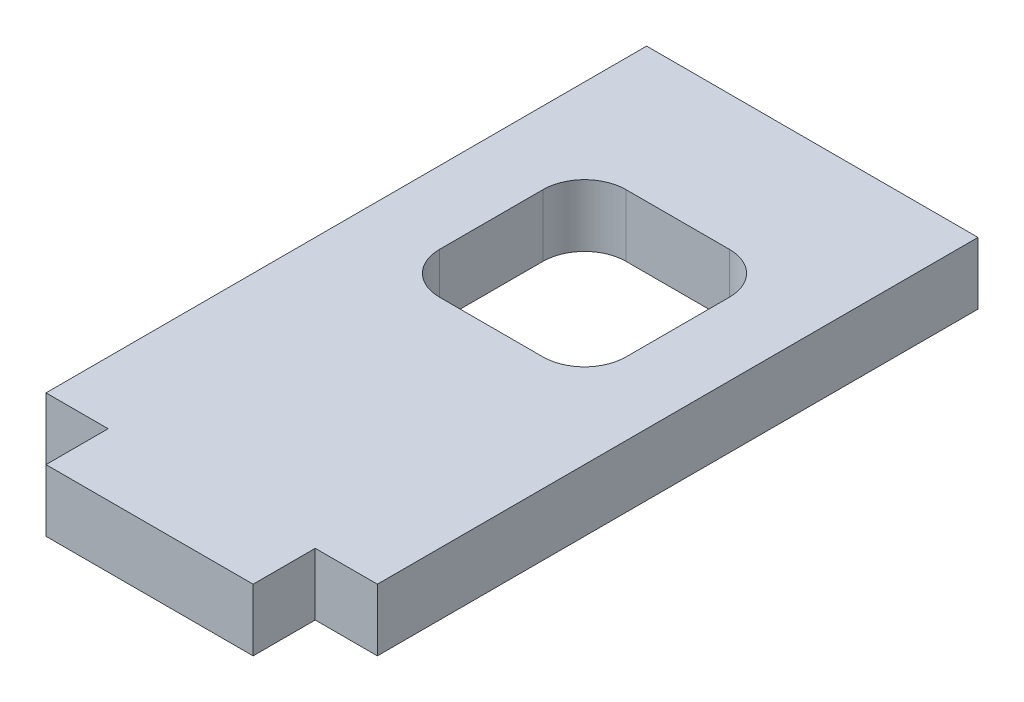
SolidWorks part; units mm, degrees
ref_plane "Plano frontal" through (0, 0, 0) normal (0, 0, 1) x (1, 0, 0)
ref_plane "Plano superior" through (0, 0, 0) normal (0, 1, 0) x (1, 0, 0)
ref_plane "Plano direito" through (0, 0, 0) normal (1, 0, 0) x (0, 0, -1)
sketch "Sketch1" plane through (0, 0, 0) normal (0, 1, 0) x (1, 0, 0)
  line L1 (-8, 14.5) -> (8, 14.5)
  line L2 (-8, 14.5) -> (-8, -14.5)
  line L3 (-8, -14.5) -> (8, -14.5)
  line L4 (8, 14.5) -> (8, -14.5)
  point P4 (0, 14.5)
  point P6 (-8, 0)
  dimension "D1" = 16
  dimension "D2" = 29
extrude "Boss-Extrude1" add sketch "Sketch1" along normal mid plane 3
sketch "Sketch2" plane through (0, 0, 0) normal (0, 1, 0) x (1, 0, 0)
  line L0 (-8, -14.5) -> (8, -14.5) construction
  line L1 (-5, -14.5) -> (5, -14.5)
  line L2 (-5, -14.5) -> (-5, -17.5)
  line L3 (-5, -17.5) -> (5, -17.5)
  line L4 (5, -14.5) -> (5, -17.5)
  line L5 (-8, 14.5) -> (-8, -14.5) construction
  line L6 (8, -14.5) -> (8, 14.5) construction
  point P6 (0, -14.5)
  dimension "D1" = 3
  dimension "D2" = 3
  dimension "D3" = 10
  dimension "D4" = 3
extrude "Boss-Extrude2" add sketch "Sketch2" along normal mid plane 3
sketch "Sketch3" plane through (0, 0, 0) normal (0, 1, 0) x (1, 0, 0)
  line L0 (-8, -14.5) -> (-5, -14.5) construction
  line L1 (-4.5, 8) -> (4.5, 8)
  line L2 (-4.5, 8) -> (-4.5, -1)
  line L3 (-4.5, -1) -> (4.5, -1)
  line L4 (4.5, 8) -> (4.5, -1)
  point P4 (-4.5, 3.5)
  point P7 (0, -1)
  dimension "D1" = 18
  dimension "D2" = 9
  dimension "D3" = 9
extrude "Cut-Extrude1" cut sketch "Sketch3" against normal through all both and the other way through all
fillet "Fillet1" radius 2 4 edges at (4.5, 0, 1) (4.5, 0, -8) (-4.5, 0, -8) (-4.5, 0, 1)
